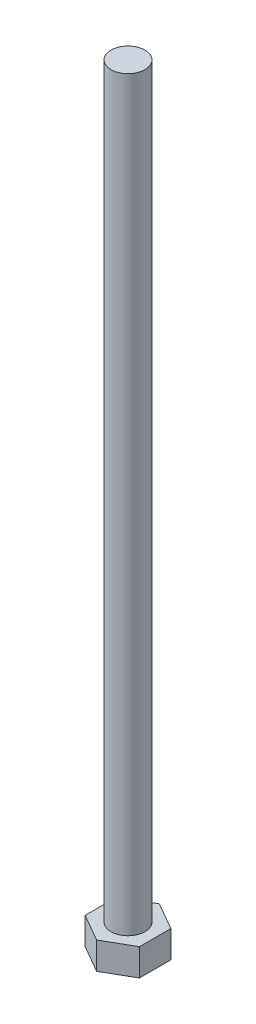
SolidWorks part; units mm, degrees
ref_plane "Спереди" through (0, 0, 0) normal (0, 0, 1) x (1, 0, 0)
ref_plane "Сверху" through (0, 0, 0) normal (0, 1, 0) x (1, 0, 0)
ref_plane "Справа" through (0, 0, 0) normal (1, 0, 0) x (0, 0, -1)
sketch "Эскиз2" plane through (0, 0, 0) normal (0, 1, 0) x (1, 0, 0)
  line L1 (4, -2.3094) -> (4, 2.3094)
  line L2 (4, 2.3094) -> (0, 4.6188)
  line L3 (0, 4.6188) -> (-4, 2.3094)
  line L4 (-4, 2.3094) -> (-4, -2.3094)
  line L5 (-4, -2.3094) -> (0, -4.6188)
  line L6 (0, -4.6188) -> (4, -2.3094)
  circle A0 centre (0, 0) radius 4 construction
extrude "Бобышка-Вытянуть1" add sketch "Эскиз2" along normal blind 4
sketch "Эскиз3" plane through (0, 4, 0) normal (0, 1, 0) x (1, 0, 0)
  circle A0 centre (0, 0) radius 2.5
extrude "Бобышка-Вытянуть2" add sketch "Эскиз3" along normal blind 110
